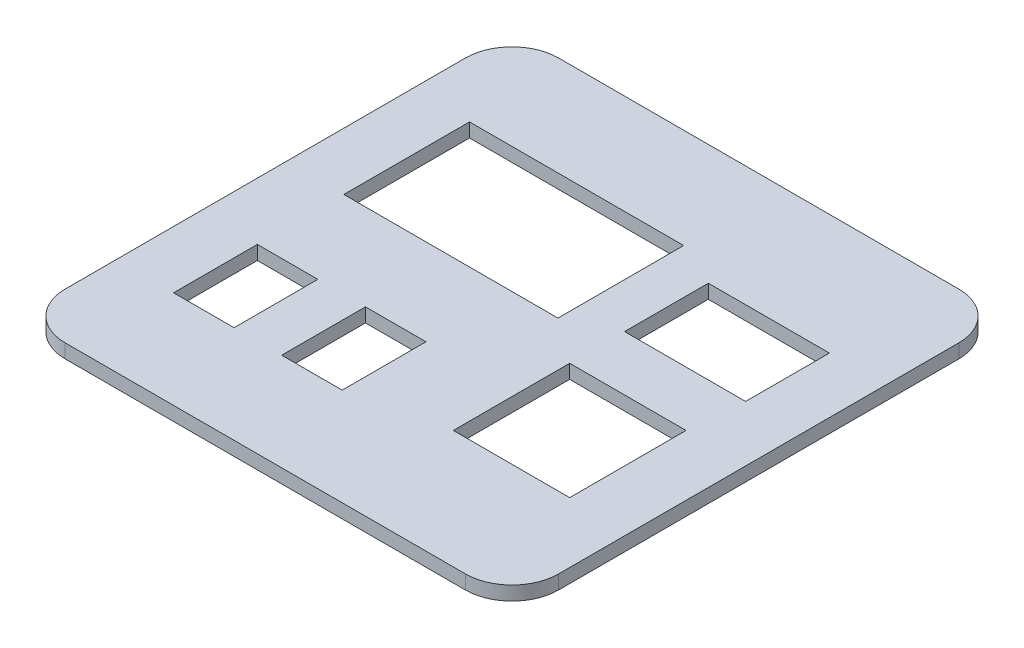
SolidWorks part; units mm, degrees
ref_plane "Front Plane" through (0, 0, 0) normal (0, 0, 1) x (1, 0, 0)
ref_plane "Top Plane" through (0, 0, 0) normal (0, 1, 0) x (1, 0, 0)
ref_plane "Right Plane" through (0, 0, 0) normal (1, 0, 0) x (0, 0, -1)
sketch "Sketch1" plane through (0, 0, 0) normal (0, 1, 0) x (1, 0, 0)
  line L0 (-40.6658, 31.5389) -> (5.3342, 31.5389)
  line L1 (-43, -53) -> (43, -53)
  line L2 (-53, -43) -> (-53, 43)
  line L3 (-43, 53) -> (43, 53)
  line L4 (53, -43) -> (53, 43)
  line L5 (-53, -53) -> (53, 53) construction
  line L6 (-53, 53) -> (53, -53) construction
  line L7 (-40, -50) -> (40, -50)
  line L8 (-50, -40) -> (-50, 40)
  line L9 (-40, 50) -> (40, 50)
  line L10 (50, -40) -> (50, 40)
  line L11 (-50, -50) -> (50, 50) construction
  line L12 (-50, 50) -> (50, -50) construction
  line L13 (5.3342, 31.5389) -> (5.3342, 4.5389)
  line L14 (5.3342, 4.5389) -> (-40.6658, 4.5389)
  line L15 (-40.6658, 4.5389) -> (-40.6658, 31.5389)
  line L16 (41, 27.1851) -> (15, 27.1851)
  line L17 (15, 27.1851) -> (15, 9.1851)
  line L18 (15, 9.1851) -> (41, 9.1851)
  line L19 (41, 9.1851) -> (41, 27.1851)
  line L20 (-40.6658, -14.046) -> (-27.6658, -14.046)
  line L21 (15, -27.6091) -> (40, -27.6091)
  line L22 (15, -27.6091) -> (15, -2.6091)
  line L23 (15, -2.6091) -> (40, -2.6091)
  line L24 (40, -27.6091) -> (40, -2.6091)
  line L25 (15, -39.046) -> (40, -14.046) construction
  line L26 (15, -14.046) -> (40, -39.046) construction
  line L27 (-27.6658, -14.046) -> (-27.6658, -32.046)
  line L28 (-27.6658, -32.046) -> (-40.6658, -32.046)
  line L29 (-40.6658, -32.046) -> (-40.6658, -14.046)
  line L30 (-17.4347, -14.046) -> (-4.4347, -14.046)
  line L31 (-4.4347, -14.046) -> (-4.4347, -32.046)
  line L32 (-4.4347, -32.046) -> (-17.4347, -32.046)
  line L33 (-17.4347, -32.046) -> (-17.4347, -14.046)
  arc A0 (43, -53) -> (53, -43) centre (43, -43) ccw
  arc A1 (-43, -53) -> (-53, -43) centre (-43, -43) cw
  arc A2 (-53, 43) -> (-43, 53) centre (-43, 43) cw
  arc A3 (43, 53) -> (53, 43) centre (43, 43) cw
  arc A4 (40, -50) -> (50, -40) centre (40, -40) ccw
  arc A5 (-40, -50) -> (-50, -40) centre (-40, -40) cw
  arc A6 (-50, 40) -> (-40, 50) centre (-40, 40) cw
  arc A7 (40, 50) -> (50, 40) centre (40, 40) cw
  point P0 (0, 0)
  point P18 (0, 0)
  point P41 (27.5, -26.546)
  dimension "D3" = 10
  dimension "D6" = 10
  dimension "D1" = 106
  dimension "D2" = 106
  dimension "D4" = 100
  dimension "D5" = 100
  dimension "D7" = 25
  dimension "D8" = 25
extrude "Boss-Extrude1" add sketch "Sketch1" along normal blind 3 contours A7 L9 A6 L8 A5 L7 A4 L10 L24 L21 L22 L23 L19 L18 L17 L16 L14 L15 L0 L13 L28 L29 L20 L27 L32 L33 L30 L31 | A3 L3 A2 L2 A1 L1 A0 L4 L9 A7 L10 A4 L7 A5 L8 A6
